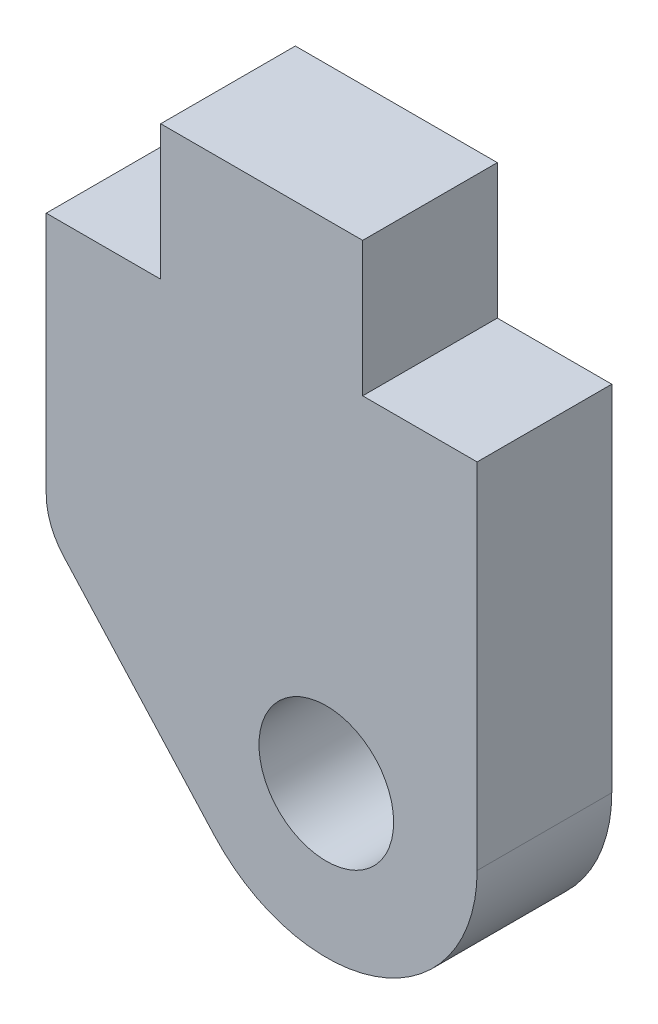
SolidWorks part; units mm, degrees
ref_plane "Front Plane" through (0, 0, 0) normal (0, 0, 1) x (1, 0, 0)
ref_plane "Top Plane" through (0, 0, 0) normal (0, 1, 0) x (1, 0, 0)
ref_plane "Right Plane" through (0, 0, 0) normal (1, 0, 0) x (0, 0, -1)
sketch "Sketch1" plane through (0, 0, 0) normal (0, 0, 1) x (1, 0, 0)
  line L0 (-5.08, 0) -> (5.08, 0) construction
  line L1 (-5.08, 0) -> (-5.08, -5.7379)
  line L2 (5.08, 0) -> (5.08, -8.3439)
  line L3 (-4.6691, -6.8037) -> (-1.1115, -10.7312)
  line L4 (-5.08, 0) -> (-2.3813, 0)
  line L5 (-2.3813, 0) -> (2.3813, 0) construction
  line L6 (-2.3813, 0) -> (-2.3813, 3.175)
  line L7 (-2.3813, 3.175) -> (2.3813, 3.175)
  line L8 (2.3813, 0) -> (2.3813, 3.175)
  line L9 (2.3813, 0) -> (5.08, 0)
  arc A0 (5.08, -8.3439) -> (-1.1115, -10.7312) centre (1.524, -8.3439) cw
  circle A1 centre (1.524, -8.3439) radius 1.5875
  arc A2 (-4.6691, -6.8037) -> (-5.08, -5.7379) centre (-3.4925, -5.7379) cw
  point P4 (0, 0)
  point P12 (-5.08, -6.35)
  dimension "D4" = 3.556
  dimension "D5" = 3.175
  dimension "D6" = 1.5875
  dimension "D1" = 10.16
  dimension "D2" = 6.35
  dimension "D3" = 8.3439
  dimension "D7" = 4.7625
  dimension "D8" = 3.175
  dimension "D9" = 2.3813
extrude "Boss-Extrude1" add sketch "Sketch1" along normal mid plane 3.175 contours A0 L2 L0 L1 L3 A1
equation "\"D9@Sketch1\"=\"D7@Sketch1\"/2"
